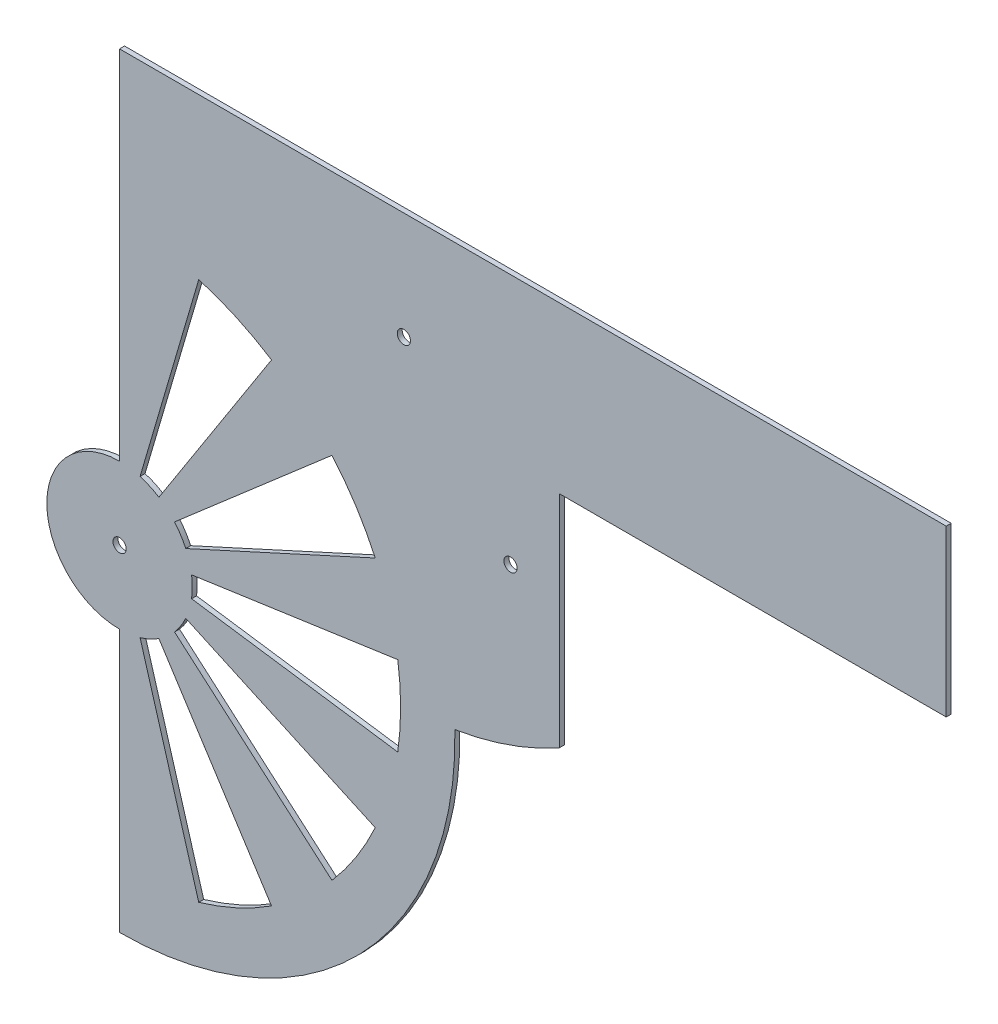
SolidWorks part; units mm, degrees
ref_plane "Front Plane" through (0, 0, 0) normal (0, 0, 1) x (1, 0, 0)
ref_plane "Top Plane" through (0, 0, 0) normal (0, 1, 0) x (1, 0, 0)
ref_plane "Right Plane" through (0, 0, 0) normal (1, 0, 0) x (0, 0, -1)
sketch "Sketch1" plane through (0, 0, 0) normal (0, 0, 1) x (1, 0, 0)
  line L0 (0, 80) -> (120.6898, 80) construction
  line L1 (0, 85) -> (120.6898, 85) construction
  line L2 (0, 130) -> (0, 22)
  line L3 (0, 31.75) -> (175.0083, 31.75) construction
  line L4 (0, -22) -> (0, -101.4262)
  line L5 (0, 130) -> (250, 130)
  line L6 (250, 130) -> (250, 80)
  line L7 (250, 80) -> (132.984, 80)
  line L8 (132.984, 80) -> (132.984, 13.418)
  circle A0 centre (0, 0) radius 2
  circle A1 centre (0, 0) radius 130 construction
  circle A2 centre (0, 0) radius 88.9 construction
  circle A3 centre (85.977, 97.5087) radius 31.75 construction
  circle A4 centre (85.977, 97.5087) radius 12.35 construction
  circle A5 centre (0, 0) radius 80 construction
  circle A6 centre (0, 0) radius 6.35 construction
  circle A7 centre (85.977, 97.5087) radius 2
  arc A8 (0, 22) -> (0, -22) centre (0, 0) ccw
  arc A9 (0, -101.4262) -> (101.3975, 2.4135) centre (0, 0) ccw
  arc A10 (101.3975, 2.4135) -> (132.984, 13.418) centre (85.977, 97.5087) ccw
  circle A11 centre (0, 0) radius 31.75 construction
  circle A12 centre (118.2321, 54.0479) radius 6.35 construction
  circle A13 centre (118.2321, 54.0479) radius 20 construction
  circle A14 centre (118.2321, 54.0479) radius 2
  dimension "D1" = 260
  dimension "D2" = 4
  dimension "D3" = 5
  dimension "D4" = 20
  dimension "D5" = 250
extrude "Boss-Extrude1" add sketch "Sketch1" along normal blind 1.5
sketch "Sketch2" plane through (0, 0, 1.5) normal (0, 0, 1) x (1, 0, 0)
  line L2 (6.1981, -21.1088) -> (23.9473, -81.5569)
  line L3 (11.8941, -18.5076) -> (45.9545, -71.5066)
  line L4 (16.6265, -14.4069) -> (64.2387, -55.6632)
  line L5 (20.0119, -9.1391) -> (77.3187, -35.3103)
  line L6 (21.7761, -3.1309) -> (84.1348, -12.0968)
  line L7 (21.7761, 3.1309) -> (84.1348, 12.0968)
  line L8 (20.0119, 9.1391) -> (77.3187, 35.3103)
  line L9 (16.6265, 14.4069) -> (64.2387, 55.6632)
  line L10 (11.8941, 18.5076) -> (45.9545, 71.5066)
  line L11 (6.1981, 21.1088) -> (23.9473, 81.5569)
  line L13 (0, -22) -> (0, -85) [skipped]
  line L14 (0, 22) -> (0, 85) [skipped]
  arc A0 (6.1981, -21.1088) -> (11.8941, -18.5076) centre (0, 0) ccw
  arc A1 (23.9473, -81.5569) -> (45.9545, -71.5066) centre (0, 0) ccw
  arc A2 (16.6265, -14.4069) -> (20.0119, -9.1391) centre (0, 0) ccw
  arc A3 (21.7761, -3.1309) -> (21.7761, 3.1309) centre (0, 0) ccw
  arc A4 (20.0119, 9.1391) -> (16.6265, 14.4069) centre (0, 0) ccw
  arc A5 (11.8941, 18.5076) -> (6.1981, 21.1088) centre (0, 0) ccw
  arc A6 (45.9545, 71.5066) -> (23.9473, 81.5569) centre (0, 0) ccw
  arc A7 (77.3187, 35.3103) -> (64.2387, 55.6632) centre (0, 0) ccw
  arc A8 (84.1348, -12.0968) -> (84.1348, 12.0968) centre (0, 0) ccw
  arc A9 (64.2387, -55.6632) -> (77.3187, -35.3103) centre (0, 0) ccw
extrude "Cut-Extrude1" cut sketch "Sketch2" against normal through all
